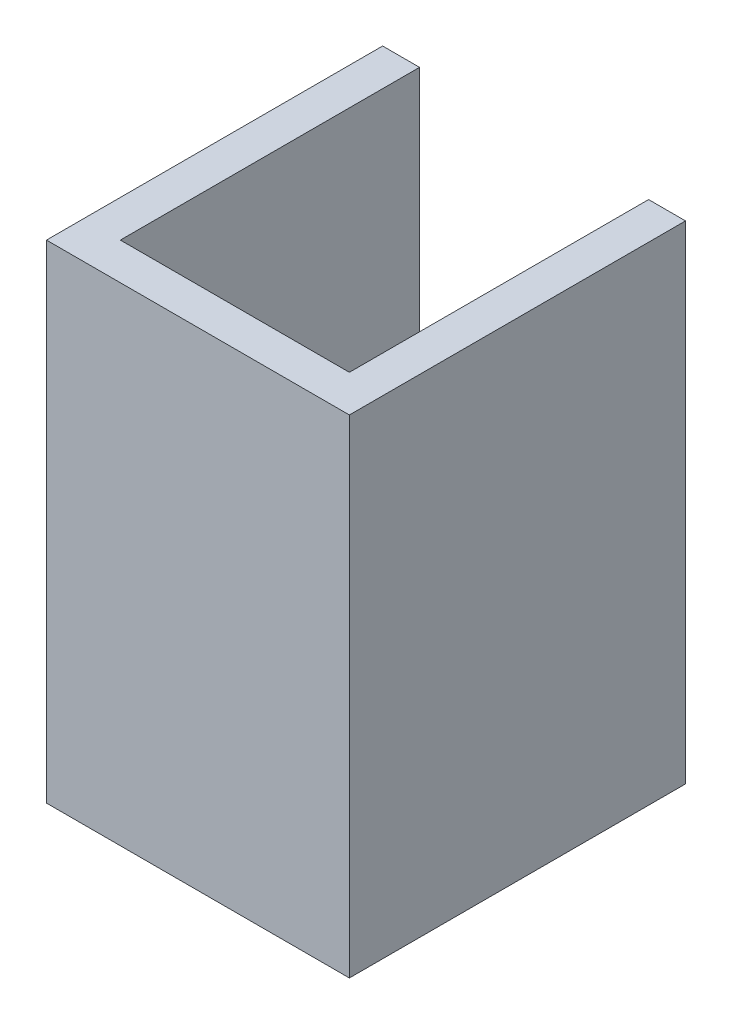
SolidWorks part; units mm, degrees
ref_plane "前视基准面" through (0, 0, 0) normal (0, 0, 1) x (1, 0, 0)
ref_plane "上视基准面" through (0, 0, 0) normal (0, 1, 0) x (1, 0, 0)
ref_plane "右视基准面" through (0, 0, 0) normal (1, 0, 0) x (0, 0, -1)
sketch "草图1" plane through (0, 0, 0) normal (0, 0, 1) x (1, 0, 0)
  line L0 (-8.0045, 14.0229) -> (4.3955, 14.0229)
  line L1 (-8.0045, 14.0229) -> (-8.0045, -8.3771)
  line L2 (-8.0045, -8.3771) -> (4.3955, -8.3771)
  line L3 (4.3955, -8.3771) -> (4.3955, 14.0229)
  line L4 (-6.0045, 16.0229) -> (2.3955, 16.0229)
  line L5 (-10.0045, 14.0229) -> (-10.0045, -10.3771)
  line L6 (-8.0045, 14.0229) -> (-8.0045, 16.0229)
  line L7 (6.3955, 14.0229) -> (6.3955, -10.3771)
  line L8 (-10.0045, -10.3771) -> (6.3955, -10.3771)
  line L9 (-10.0045, 14.0229) -> (-10.0045, 16.0229)
  line L10 (-10.0045, 16.0229) -> (-6.0045, 16.0229)
  line L11 (-6.0045, 16.0229) -> (-6.0045, 14.0229)
  line L12 (6.3955, 14.0229) -> (6.3955, 16.0229)
  line L13 (6.3955, 16.0229) -> (2.3955, 16.0229)
  line L14 (2.3955, 16.0229) -> (2.3955, 14.0229)
  line L15 (4.3955, 14.0229) -> (4.3955, 16.0229)
extrude "凸台-拉伸1" add sketch "草图1" along normal blind 16.2 contours L13 L14 L0 L3 L2 L1 L11 L10 L9 L5 L8 L7 L12
sketch "草图4" plane through (0, 0, 16.2) normal (0, 0, 1) x (1, 0, 0)
  line L0 (-10.0045, 16.0229) -> (6.3955, 16.0229)
  line L1 (6.3955, 16.0229) -> (6.3955, -10.3771)
  line L2 (6.3955, -10.3771) -> (-10.0045, -10.3771)
  line L3 (-10.0045, -10.3771) -> (-10.0045, 16.0229)
extrude "凸台-拉伸2" add sketch "草图4" along normal blind 2 contours L3 L0 L1 L2
sketch "草图5" plane through (0, 0, 16.2) normal (0, 0, -1) x (-1, 0, 0)
sketch "草图6" plane through (4.3955, 0, 0) normal (-1, 0, 0) x (0, 0, 1)
  line L0 (16.2, 16.0229) -> (16.2, 26.0229)
  line L1 (0, 16.0229) -> (0, 26.0229)
  line L2 (0, 26.0229) -> (16.2, 26.0229)
  line L3 (0, 16.0229) -> (16.2, 16.0229)
  line L4 (16.2, 26.0229) -> (16.2, 36.0229)
  line L5 (16.2, 36.0229) -> (0, 36.0229)
  line L6 (0, 36.0229) -> (0, 26.0229)
  line L7 (16.2, 16.0229) -> (18.2, 16.0229)
  line L8 (18.2, 16.0229) -> (18.2, 19.0229)
  line L9 (18.2, 19.0229) -> (16.2, 19.0229)
  line L10 (18.2, 19.0229) -> (18.2, 25.0229)
  line L11 (18.2, 25.0229) -> (16.2, 25.0229)
  line L12 (16.2, 25.0229) -> (16.2, 19.0229)
